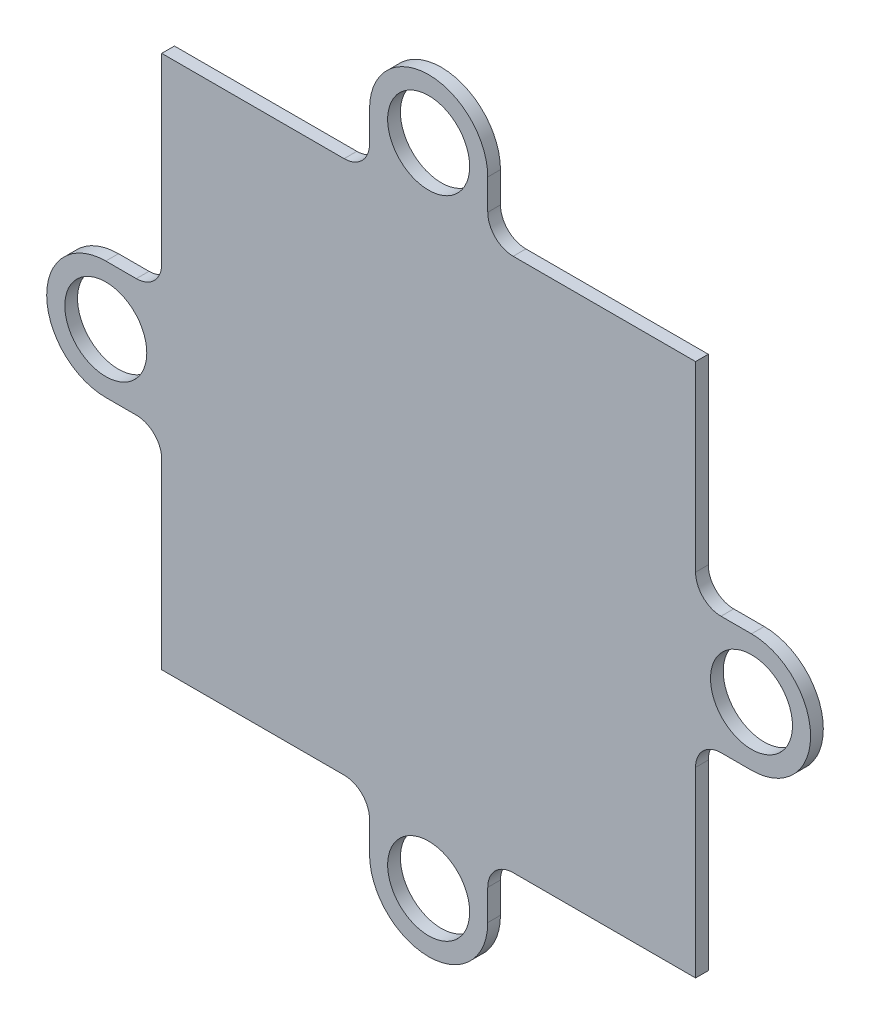
SolidWorks part; units mm, degrees
ref_plane "Front Plane" through (0, 0, 0) normal (0, 0, 1) x (1, 0, 0)
ref_plane "Top Plane" through (0, 0, 0) normal (0, 1, 0) x (1, 0, 0)
ref_plane "Right Plane" through (0, 0, 0) normal (1, 0, 0) x (0, 0, -1)
sketch "Sketch1" plane through (0, 0, 0) normal (0, 0, 1) x (1, 0, 0)
  line L0 (-4.65, 25.4) -> (-4.65, 23)
  line L1 (-21, -21) -> (-6.65, -21)
  line L2 (-21, -21) -> (-21, -6.65)
  line L3 (-21, 21) -> (-6.65, 21)
  line L4 (21, -21) -> (21, -6.65)
  line L5 (-21, -21) -> (21, 21) construction
  line L6 (-21, 21) -> (21, -21) construction
  line L7 (-6.65, 21) -> (-8.7591, 21)
  line L8 (4.65, 25.4) -> (4.65, 23)
  line L9 (6.65, 21) -> (7.1335, 21)
  line L10 (25.4, 4.65) -> (23, 4.65)
  line L11 (21, 6.65) -> (21, 8.7591)
  line L12 (25.4, -4.65) -> (23, -4.65)
  line L13 (21, -6.65) -> (21, -7.1335)
  line L14 (4.65, -25.4) -> (4.65, -23)
  line L15 (6.65, -21) -> (8.7591, -21)
  line L16 (-4.65, -25.4) -> (-4.65, -23)
  line L17 (-6.65, -21) -> (-7.1335, -21)
  line L18 (-25.4, -4.65) -> (-23, -4.65)
  line L19 (-21, -6.65) -> (-21, -8.7591)
  line L20 (-25.4, 4.65) -> (-23, 4.65)
  line L21 (-21, 6.65) -> (-21, 7.1335)
  line L22 (-21, 6.65) -> (-21, 21)
  line L23 (6.65, 21) -> (21, 21)
  line L24 (21, 6.65) -> (21, 21)
  line L25 (6.65, -21) -> (21, -21)
  circle A0 centre (0, 25.4) radius 3.225
  arc A1 (4.65, 25.4) -> (-4.65, 25.4) centre (0, 25.4) ccw
  arc A2 (4.65, 23) -> (6.65, 21) centre (6.65, 23) ccw
  arc A3 (-4.65, 23) -> (-6.65, 21) centre (-6.65, 23) cw
  circle A4 centre (25.4, 0) radius 3.225
  arc A5 (25.4, -4.65) -> (25.4, 4.65) centre (25.4, 0) ccw
  arc A6 (23, -4.65) -> (21, -6.65) centre (23, -6.65) ccw
  arc A7 (23, 4.65) -> (21, 6.65) centre (23, 6.65) cw
  circle A8 centre (0, -25.4) radius 3.225
  arc A9 (-4.65, -25.4) -> (4.65, -25.4) centre (0, -25.4) ccw
  arc A10 (-4.65, -23) -> (-6.65, -21) centre (-6.65, -23) ccw
  arc A11 (4.65, -23) -> (6.65, -21) centre (6.65, -23) cw
  circle A12 centre (-25.4, 0) radius 3.225
  arc A13 (-25.4, 4.65) -> (-25.4, -4.65) centre (-25.4, 0) ccw
  arc A14 (-23, 4.65) -> (-21, 6.65) centre (-23, 6.65) ccw
  arc A15 (-23, -4.65) -> (-21, -6.65) centre (-23, -6.65) cw
  point P0 (0, 0)
  point P53 (0, 0)
  dimension "D1" = 2
extrude "Boss-Extrude1" add sketch "Sketch1" along normal blind 1 contours L18 A15 L2 L1 A10 L16 A9 L14 A11 L15 L25 L4 A6 L12 A5 L10 A7 L11 L24 L23 L9 A2 L8 A1 L0 A3 L3 L22 L21 A14 L20 A13 A0 A4 A8 A12
